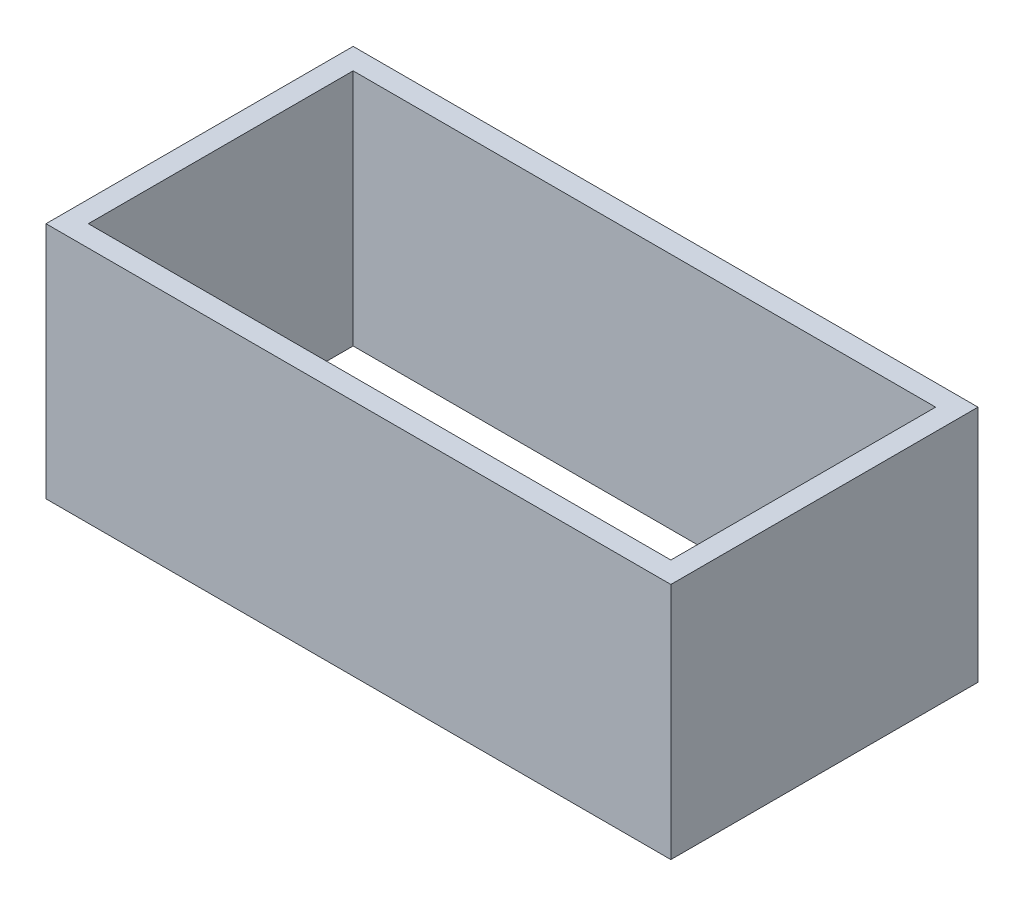
SolidWorks part; units mm, degrees
ref_plane "Front Plane" through (0, 0, 0) normal (0, 0, 1) x (1, 0, 0)
ref_plane "Top Plane" through (0, 0, 0) normal (0, 1, 0) x (1, 0, 0)
ref_plane "Right Plane" through (0, 0, 0) normal (1, 0, 0) x (0, 0, -1)
sketch "Sketch1" plane through (0, 0, 0) normal (0, 1, 0) x (1, 0, 0)
  line L0 (-29.5, -14.5) -> (-29.5, 14.5)
  line L1 (27.5, -12.5) -> (-27.5, -12.5)
  line L2 (27.5, -12.5) -> (27.5, 12.5)
  line L3 (27.5, 12.5) -> (-27.5, 12.5)
  line L4 (-27.5, -12.5) -> (-27.5, 12.5)
  line L5 (27.5, -12.5) -> (-27.5, 12.5) construction
  line L6 (27.5, 12.5) -> (-27.5, -12.5) construction
  line L7 (29.5, 14.5) -> (-29.5, 14.5)
  line L8 (29.5, -14.5) -> (29.5, 14.5)
  line L9 (29.5, -14.5) -> (-29.5, -14.5)
  point P0 (0, 0)
  dimension "D1" = 25
  dimension "D2" = 55
  dimension "D3" = 2
extrude "Boss-Extrude1" add sketch "Sketch1" along normal blind 22.5
